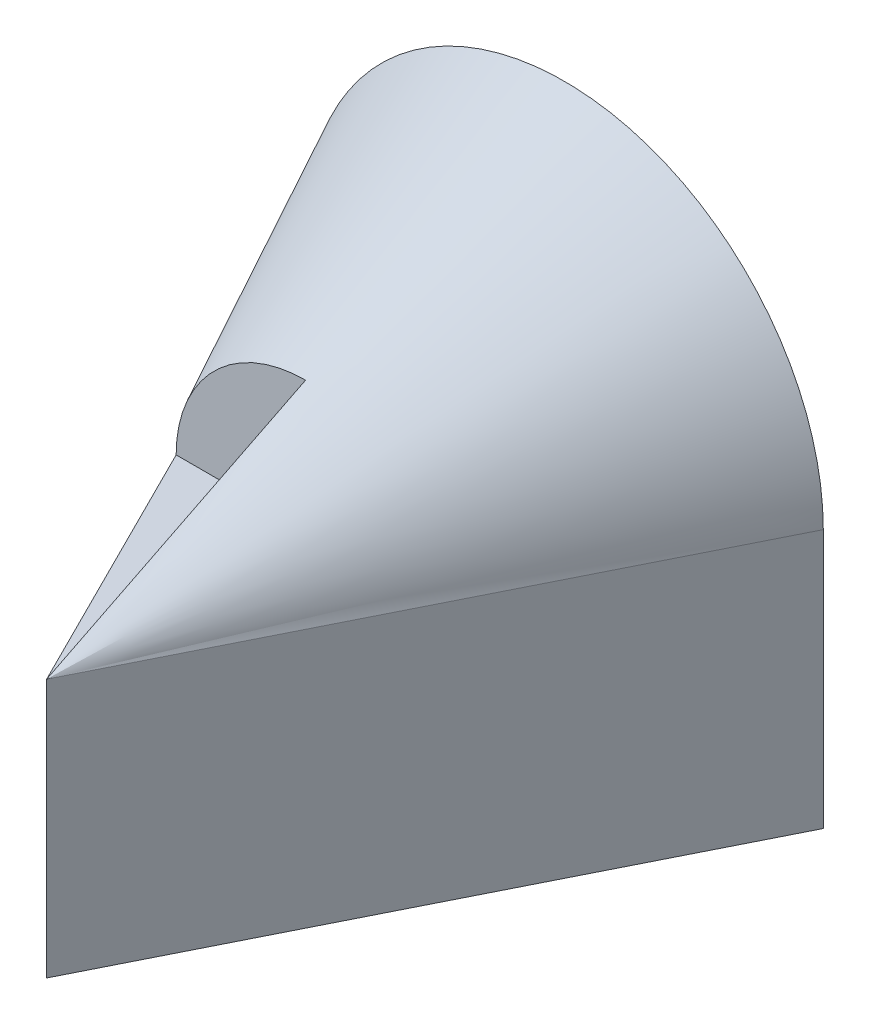
SolidWorks part; units mm, degrees
ref_plane "Front Plane" through (0, 0, 0) normal (0, 0, 1) x (1, 0, 0)
ref_plane "Top Plane" through (0, 0, 0) normal (0, 1, 0) x (1, 0, 0)
ref_plane "Right Plane" through (0, 0, 0) normal (1, 0, 0) x (0, 0, -1)
sketch "Sketch1" plane through (0, 0, 0) normal (0, 0, 1) x (1, 0, 0)
  line L1 (0, 0) -> (40, 0)
  line L2 (0, 0) -> (0, 20)
  line L3 (0, 20) -> (40, 20)
  line L4 (40, 0) -> (40, 20)
  arc A0 (40, 20) -> (0, 20) centre (20, 20) ccw
  dimension "D1" = 40
  dimension "D2" = 20
extrude "Boss-Extrude1" add sketch "Sketch1" along normal blind 40 contours L3 A0 | L1 L4 L3 L2
sketch "Sketch4" plane through (0, 0, 40) normal (0, 0, 1) x (1, 0, 0)
  line L0 (20, 30) -> (20, 20)
  line L1 (20, 20) -> (10, 20)
  arc A0 (20, 30) -> (10, 20) centre (20, 20) ccw
  dimension "D1" = 10
  dimension "D2" = 10
  dimension "D3" = 0
extrude "Cut-Extrude18" cut sketch "Sketch4" against normal blind 20
sketch "Sketch11" plane through (0, 0, 0) normal (0, 1, 0) x (1, 0, 0)
  line L0 (0, 0) -> (20, -40)
  line L1 (20, -40) -> (40, 0)
  line L2 (40, 0) -> (40, -40)
  line L3 (40, -40) -> (0, -40)
  line L4 (0, -40) -> (0, 0)
extrude "Cut-Extrude20" cut sketch "Sketch11" along normal blind 59 contours L4 L3 L0 | L3 L2 L1
sketch "Sketch12" plane through (0, 0, 0) normal (1, 0, 0) x (0, 0, -1)
  line L0 (-40, 20) -> (0, 40)
  line L1 (0, 40) -> (-40, 40)
  line L2 (-40, 40) -> (-40, 20)
extrude "Cut-Extrude21" cut sketch "Sketch12" along normal blind 59
sketch "Sketch13" plane through (0, 20, 0) normal (0, 1, 0) x (1, 0, 0)
  line L1 (-2.1234, -71.233) -> (54.1089, -71.233)
  line L2 (-2.1234, -71.233) -> (-2.1234, 60.4935)
  line L3 (-2.1234, 60.4935) -> (54.1089, 60.4935)
  line L4 (54.1089, -71.233) -> (54.1089, 60.4935)
extrude "Cut-Extrude22" cut sketch "Sketch13" along normal blind 20
sketch "Sketch14" plane through (0, 20, 0) normal (0, 1, 0) x (1, 0, 0)
  line L0 (20, -40) -> (20, 0)
  line L1 (0, 0) -> (40, 0) construction
  line L2 (20, 0) -> (0, 0)
  line L3 (0, 0) -> (20, -40)
revolve "Revolve1" add sketch "Sketch14" angle 180 about L0
ref_plane "Plane1" through (0, 20, 0) normal (0, 1, 0) x (1, 0, 0)
sketch "Sketch15" plane through (0, 20, 0) normal (0, 1, 0) x (1, 0, 0)
  line L0 (20, -40) -> (20, -20)
  line L1 (20, -20) -> (10, -20)
  line L2 (0, 0) -> (20, -40) construction
  line L3 (10, -20) -> (20, -40)
  dimension "D1" = 20
extrude "Cut-Extrude23" cut sketch "Sketch15" along normal blind 20
